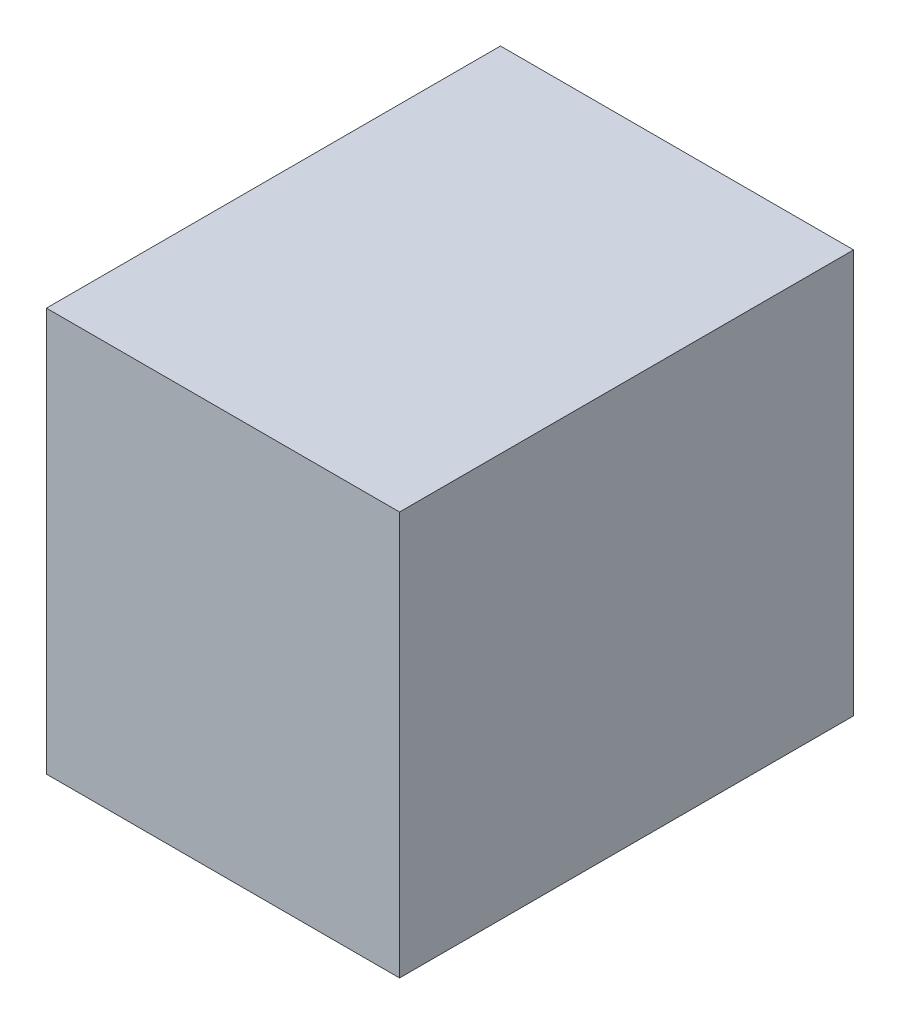
SolidWorks part; units mm, degrees
material "1023 al carbonio, lamiera (SS)"
ref_plane "Piano frontale" through (0, 0, 0) normal (0, 0, 1) x (1, 0, 0)
ref_plane "Piano superiore" through (0, 0, 0) normal (0, 1, 0) x (1, 0, 0)
ref_plane "Piano destro" through (0, 0, 0) normal (1, 0, 0) x (0, 0, -1)
sketch "Schizzo1" plane through (0, 0, 0) normal (0, 0, 1) x (1, 0, 0)
  line L0 (17.5, 40) -> (17.5, 0) construction
  line L1 (0, 0) -> (35, 0)
  line L2 (0, 0) -> (0, 40)
  line L3 (0, 40) -> (35, 40)
  line L4 (35, 0) -> (35, 40)
  dimension "D1" = 40
  dimension "D2" = 35
extrude "Estrusione-Estrusione1" add sketch "Schizzo1" along normal blind 45
